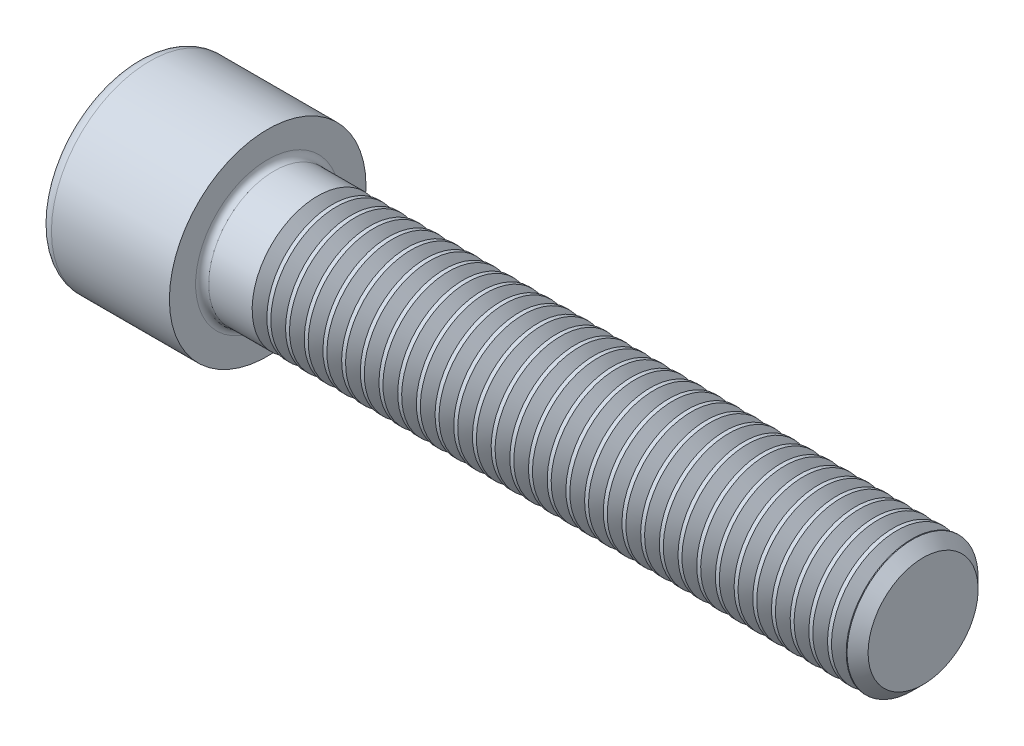
SolidWorks part; units mm, degrees
revolve "Base-Revolve" add sketch "BodySke"
sketch "BodySke" plane through (0, 0, 0) normal (0, 0, 1) x (1, 0, 0)
  line L0 (0, 0) -> (0, 9)
  line L1 (0, 9) -> (12, 9)
  line L2 (12, 9) -> (12, 6)
  line L3 (12, 6) -> (71.036, 6)
  line L4 (72, 5.036) -> (72, 0)
  line L5 (72, 0) -> (0, 0)
  line L6 (-31.75, 0) -> (127, 0) construction
  line L8 (72, 5.036) -> (71.036, 6)
  line L10 (72, -5.036) -> (71.036, -6) construction
  line L11 (13.75, 9.525) -> (13.75, 3.175) construction
  line L12 (17, 9.525) -> (17, 3.175) construction
  line L13 (12, 9.525) -> (12, 3.175) construction
cosmetic thread "ThreadCosmetic" [suppressed]
fillet "Fillet1" radius 0.6 1 edges at (12, 0, 6)
fillet "Fillet2" radius 1.2 1 edges at (0, 0, 9)
ref_plane "Plane1" through (0, 0, 0) normal (0, 0, 1) x (1, 0, 0)
ref_plane "Plane2" through (0, 0, 0) normal (0, 1, 0) x (1, 0, 0)
ref_plane "Plane3" through (0, 0, 0) normal (1, 0, 0) x (0, 0, -1)
sketch "Sketch2" plane through (0, 0, 0) normal (0, 0, 1) x (1, 0, 0)
  line L0 (0, 5.0125) -> (6, 5.0125)
  line L1 (6, 5.0125) -> (8.894, 0)
  line L2 (-31.75, 0) -> (127, 0) construction
  line L3 (8.894, 0) -> (0, 0)
  line L4 (0, 0) -> (0, 5.0125)
  line L6 (0, 0) -> (47.625, 0) construction
revolve "Hex-PreBroach" cut sketch "Sketch2" angle 360 about L6
sketch "Sketch3" plane through (0, 0, 0) normal (-1, 0, 0) x (0, 0.5, 0.866)
  line L0 (2.894, 5.0125) -> (-2.894, 5.0125)
  line L1 (-2.894, 5.0125) -> (-5.7879, 0)
  line L2 (2.894, 5.0125) -> (5.7879, 0)
  line L3 (2.894, -5.0125) -> (5.7879, 0)
  line L4 (2.894, -5.0125) -> (-2.894, -5.0125)
  line L5 (-2.894, -5.0125) -> (-5.7879, 0)
extrude "Hex" cut sketch "Sketch3" against normal blind 6
sketch "ThdSchSke" plane through (0, 0, 0) normal (0, 0, 1) x (1, 0, 0)
  line L0 (17.25, -5.036) -> (16.575, -6)
  line L1 (17.25, -5.036) -> (17.925, -6)
  line L2 (17.925, -6) -> (17.925, -7.5)
  line L3 (-3.175, 0) -> (5.1513, 0) construction
  line L4 (0, 7.8) -> (0, -7.8) construction
  line L5 (17.925, -7.5) -> (16.575, -7.5)
  line L6 (16.575, -7.5) -> (16.575, -6)
revolve "ThreadSchematic" cut sketch "ThdSchSke" angle 360 about L3
pattern_linear "ThdSchPat" count 32 spacing 1.7109 along (1, 0, 0) of "ThreadSchematic"
equation "\"D2@Sketch3\" = \"Hex_size@Sketch3\" / 2"
equation "\"D1@Sketch3\" = \"Hex_size@Sketch3\" / 2"
equation "\"D1@Sketch2\" = \"Hex_size@Sketch3\" / 2"
equation "\"Thread_minor@ThreadCosmetic\"  =  \"Minor_dia@BodySke\""
equation "\"Depth@Sketch2\" =  \"Key_eng@Hex\""
equation "\"Thread_length@ThreadCosmetic\" = ((sgn( (\"Length@BodySke\" - \"Advance@BodySke\" * 3.0) - \"Thread_nom@BodySke\" )-1)*( (\"Length@BodySke\" - \"Advance@BodySke\" * 3.0) - \"Thread_nom@BodySke\" ))/-2+ \"Thread_nom@BodySke\""
equation "\"Thread_minor@ThdSchSke\" = \"Minor_dia@BodySke\""
equation "\"Diameter@ThdSchSke\" = \"Diameter@BodySke\""
equation "\"Overcut@ThdSchSke\" = \"Diameter@BodySke\" * 1.25"
equation "\"Start@ThdSchSke\" = \"Head_ht@BodySke\" + \"Length@BodySke\" - \"Thread_length@ThreadCosmetic\"  '---Non-countersunk---"
equation "\"Num_threads@ThdSchPat\" = int( \"Thread_length@ThreadCosmetic\" / \"Advance@BodySke\" + 0.999 )  + 1"
equation "\"Advance@ThdSchPat\" = \"Thread_length@ThreadCosmetic\" /  (\"Num_threads@ThdSchPat\" - 1) 'relax it"
equation "\"Num_threads@ThdSchPat\" = \"Num_threads@ThdSchPat\" - sgn( \"Num_threads@ThdSchPat\" - 1) '---chamfered tips only---"
